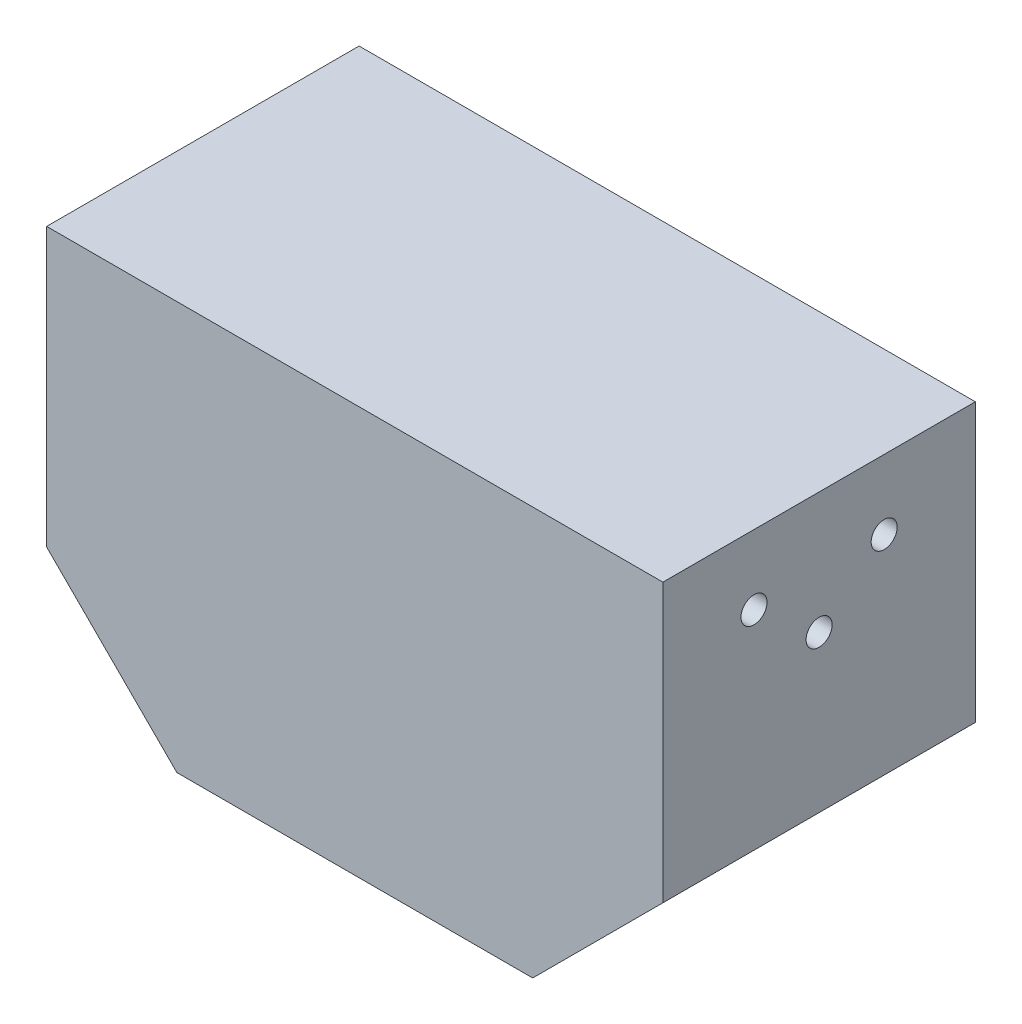
SolidWorks part; units mm, degrees
material "Свинец"
ref_plane "Спереди" through (0, 0, 0) normal (0, 0, 1) x (1, 0, 0)
ref_plane "Сверху" through (0, 0, 0) normal (0, 1, 0) x (1, 0, 0)
ref_plane "Справа" through (0, 0, 0) normal (1, 0, 0) x (0, 0, -1)
sketch "Эскиз1" plane through (0, 0, 0) normal (0, 1, 0) x (1, 0, 0)
  line L1 (-35.5, -18) -> (35.5, -18)
  line L2 (-35.5, -18) -> (-35.5, 18)
  line L3 (-35.5, 18) -> (35.5, 18)
  line L4 (35.5, -18) -> (35.5, 18)
  line L5 (-35.5, -18) -> (35.5, 18) construction
  line L6 (-35.5, 18) -> (35.5, -18) construction
  point P0 (0, 0)
  dimension "D1" = 36
  dimension "D2" = 71
extrude "Бобышка-Вытянуть1" add sketch "Эскиз1" along normal blind 47
sketch "Эскиз2" plane through (0, 0, 18) normal (0, 0, 1) x (1, 0, 0)
  line L0 (-35.5, 15) -> (-20.5, 0)
  line L1 (-35.5, 47) -> (-35.5, 0) construction
  line L2 (-35.5, 0) -> (35.5, 0) construction
  line L3 (0, 47) -> (0, 0) construction
  line L4 (21.6314, -1.759) -> (21.6314, -1.9202)
  line L5 (-35.5, 47) -> (35.5, 47) construction
  line L6 (-20.5, 0) -> (-35.5, 0)
  line L7 (-35.5, 0) -> (-35.5, 15)
  line L8 (35.5, 0) -> (35.5, 15)
  line L9 (20.5, 0) -> (35.5, 0)
  line L10 (35.5, 15) -> (20.5, 0)
  line M5 (-35.5, 0) -> (35.5, 0)
  line M6 (35.5, 0) -> (35.5, 47)
  line M8 (-35.5, 47) -> (-35.5, 0)
  dimension "D1" = 15
extrude "Вырез-Вытянуть1" cut sketch "Эскиз2" against normal through all contours L0 M8 M5 | L10 M6 M5
sketch "Эскиз3" plane through (35.5, 0, 0) normal (1, 0, 0) x (0, 0, -1)
  line L0 (-7.5, 39) -> (-18, 39) construction
  line L1 (-18, 47) -> (-18, 15) construction
  line L2 (7.5, 39) -> (18, 39) construction
  line L3 (18, 47) -> (18, 15) construction
  line L4 (-18, 47) -> (18, 47) construction
  circle A0 centre (-7.5, 39) radius 1.5
  circle A1 centre (7.5, 39) radius 1.5
  circle A2 centre (0, 33) radius 1.5
  dimension "D1" = 3
  dimension "D5" = 6
  dimension "D2" = 15
  dimension "D3" = 10.5
  dimension "D4" = 8
extrude "Вырез-Вытянуть2" cut sketch "Эскиз3" against normal blind 20
mirror "Зеркальное отражение1" about plane through (0, 0, 0) normal (1, 0, 0) of "Вырез-Вытянуть2"
